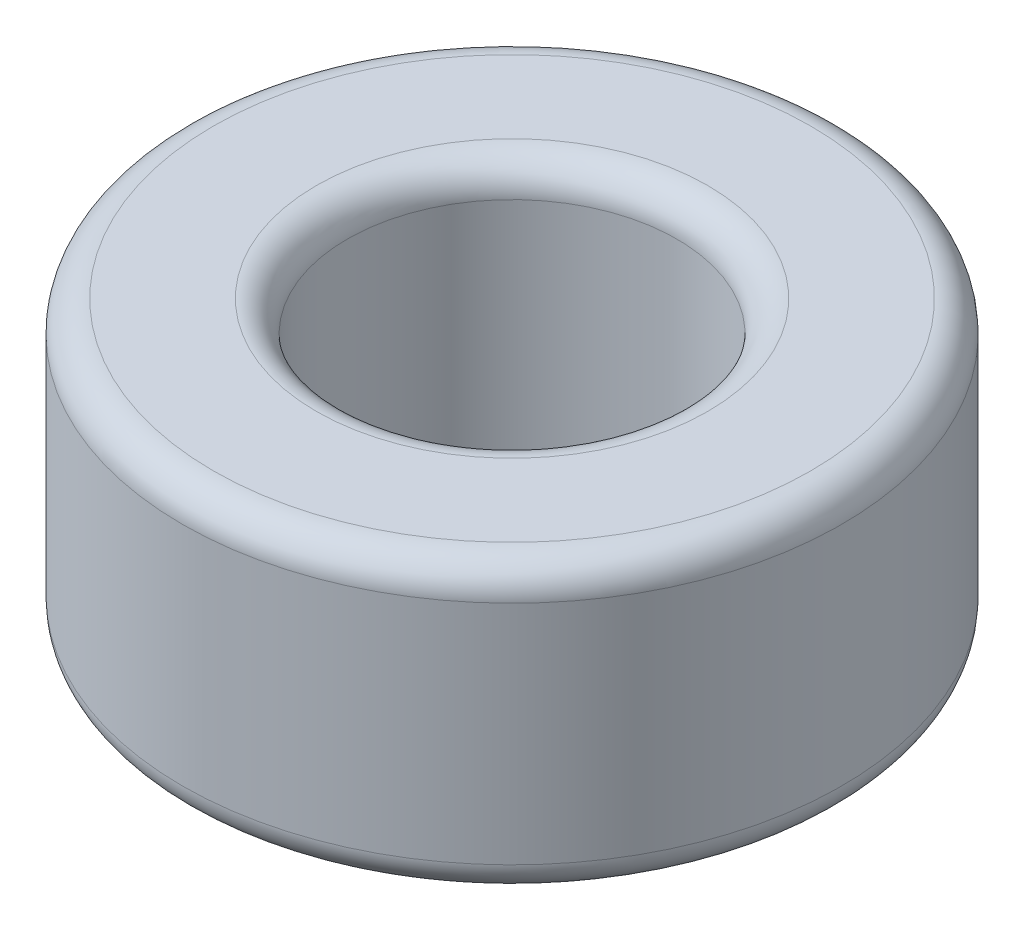
SolidWorks part; units mm, degrees
material "BUTYL"
ref_plane "Front Plane" through (0, 0, 0) normal (0, 0, 1) x (1, 0, 0)
ref_plane "Top Plane" through (0, 0, 0) normal (0, 1, 0) x (1, 0, 0)
ref_plane "Right Plane" through (0, 0, 0) normal (1, 0, 0) x (0, 0, -1)
sketch "Sketch1" plane through (0, 0, 0) normal (0, 1, 0) x (1, 0, 0)
  circle A0 centre (0, 0) radius 203.2
  dimension "D1" = 406.4
extrude "Boss-Extrude1" add sketch "Sketch1" along normal blind 177.8
sketch "Sketch2" plane through (0, 0, 0) normal (0, -1, 0) x (1, 0, 0)
  circle A0 centre (0, 0) radius 101.6
  dimension "D1" = 203.2
extrude "Cut-Extrude1" cut sketch "Sketch2" against normal through all and the other way through all
fillet "Fillet1" radius 19.05 4 edges at (0, 0, 203.2) (0, 0, 101.6) (0, 177.8, 203.2) (0, 177.8, -101.6)
shell "Shell1" thickness 12.7
